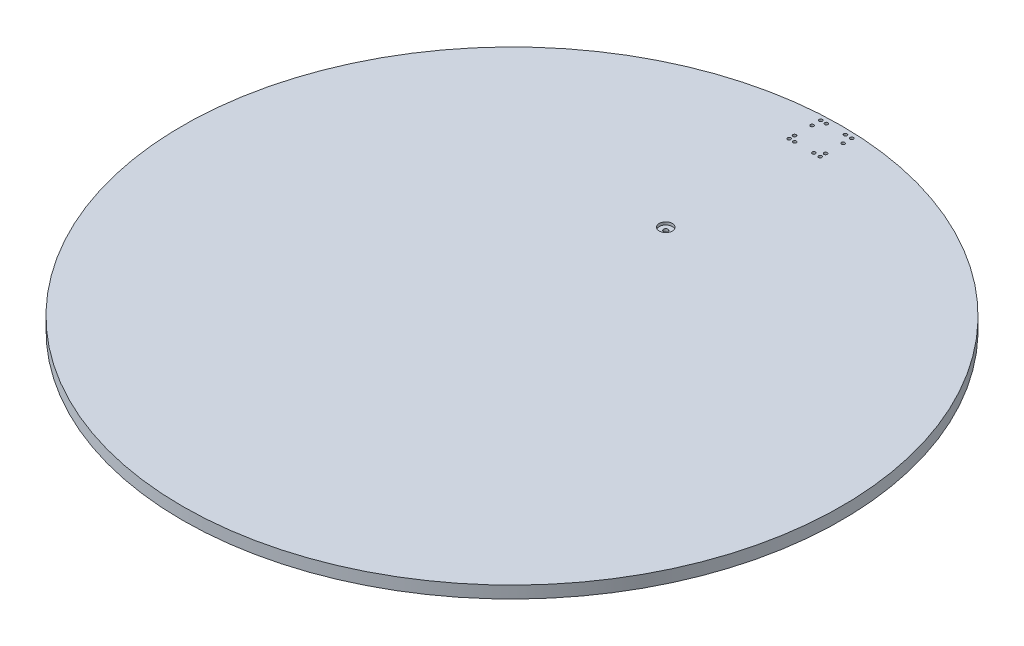
SolidWorks part; units mm, degrees
ref_plane "Plan de face" through (0, 0, 0) normal (0, 0, 1) x (1, 0, 0)
ref_plane "Plan de dessus" through (0, 0, 0) normal (0, 1, 0) x (1, 0, 0)
ref_plane "Plan de droite" through (0, 0, 0) normal (1, 0, 0) x (0, 0, -1)
sketch "Esquisse1" plane through (0, 0, 0) normal (0, 1, 0) x (1, 0, 0)
  circle A0 centre (0, 0) radius 600
extrude "Boss.-Extru.1" add sketch "Esquisse1" along normal blind 22
sketch "Esquisse2" plane through (0, 22, 0) normal (0, 1, 0) x (1, 0, 0)
  circle A0 centre (0, 280) radius 4
extrude "Enlèv. mat.-Extru.1" cut sketch "Esquisse2" against normal through all
sketch "Esquisse3" plane through (0, 0, 0) normal (0, -1, 0) x (1, 0, 0)
  line L0 (6.5, -280) -> (6.5, -276.2472) construction
  line L1 (6.5, -283.7528) -> (6.5, -280) construction
  line L2 (3.25, -285.6292) -> (6.5, -283.7528) construction
  line L3 (6.5, -276.2472) -> (3.25, -274.3708) construction
  line L4 (3.25, -274.3708) -> (0, -272.4944) construction
  line L5 (0, -272.4944) -> (-3.25, -274.3708) construction
  line L6 (-3.25, -274.3708) -> (-6.5, -276.2472) construction
  line L7 (0, -287.5056) -> (3.25, -285.6292) construction
  line L8 (-3.25, -285.6292) -> (0, -287.5056) construction
  line L9 (-6.5, -283.7528) -> (-3.25, -285.6292) construction
  line L10 (-6.5, -280) -> (-6.5, -283.7528) construction
  line L11 (-6.5, -276.2472) -> (-6.5, -280) construction
  line L12 (6.5, -280) -> (6.5, -276.2472)
  line L13 (6.5, -283.7528) -> (6.5, -280)
  line L14 (3.25, -285.6292) -> (6.5, -283.7528)
  line L15 (6.5, -276.2472) -> (3.25, -274.3708)
  line L16 (3.25, -274.3708) -> (0, -272.4944)
  line L17 (0, -272.4944) -> (-3.25, -274.3708)
  line L18 (-3.25, -274.3708) -> (-6.5, -276.2472)
  line L19 (0, -287.5056) -> (3.25, -285.6292)
  line L20 (-3.25, -285.6292) -> (0, -287.5056)
  line L21 (-6.5, -283.7528) -> (-3.25, -285.6292)
  line L22 (-6.5, -280) -> (-6.5, -283.7528)
  line L23 (-6.5, -276.2472) -> (-6.5, -280)
extrude "Enlèv. mat.-Extru.2" cut sketch "Esquisse3" against normal blind 8
sketch "Esquisse4" plane through (0, 22, 0) normal (0, 1, 0) x (1, 0, 0)
  circle A0 centre (0, 280) radius 12
extrude "Enlèv. mat.-Extru.3" cut sketch "Esquisse4" against normal blind 5
sketch "Esquisse6" plane through (0, 22, 0) normal (0, 1, 0) x (1, 0, 0)
  circle A0 centre (-27.3597, 541.7732) radius 3 construction
  circle A1 centre (-27.3597, 541.7732) radius 3
  circle A2 centre (-27.3597, 531.8831) radius 3 construction
  circle A3 centre (-27.3597, 531.8831) radius 3
  circle A4 centre (-17.3384, 531.8831) radius 3 construction
  circle A5 centre (-17.3384, 531.8831) radius 3
  circle A6 centre (-27.3597, 589.5163) radius 3 construction
  circle A7 centre (-27.3597, 573.6648) radius 3 construction
  circle A8 centre (-17.3384, 589.5163) radius 3 construction
  circle A9 centre (17.5876, 589.5163) radius 3 construction
  circle A10 centre (29.136, 589.5163) radius 3 construction
  circle A11 centre (29.136, 573.6648) radius 3 construction
  circle A12 centre (29.136, 541.7732) radius 3 construction
  circle A13 centre (29.136, 531.8831) radius 3 construction
  circle A14 centre (17.5876, 531.8831) radius 3 construction
  circle A15 centre (-27.3597, 589.5163) radius 3
  circle A16 centre (-27.3597, 573.6648) radius 3
  circle A17 centre (-17.3384, 589.5163) radius 3
  circle A18 centre (17.5876, 589.5163) radius 3
  circle A19 centre (29.136, 589.5163) radius 3
  circle A20 centre (29.136, 573.6648) radius 3
  circle A21 centre (29.136, 541.7732) radius 3
  circle A22 centre (29.136, 531.8831) radius 3
  circle A23 centre (17.5876, 531.8831) radius 3
extrude "Enlèv. mat.-Extru.4" cut sketch "Esquisse6" against normal through all
